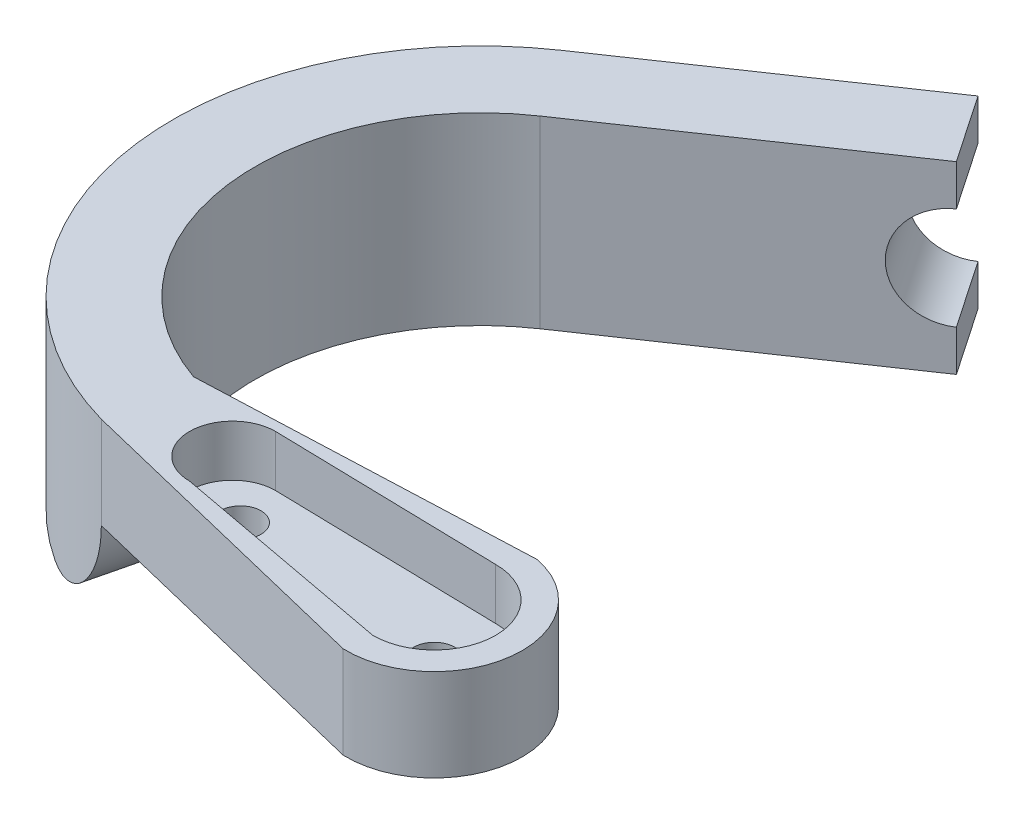
SolidWorks part; units mm, degrees
ref_plane "Front" through (0, 0, 0) normal (0, 0, 1) x (1, 0, 0)
ref_plane "Top" through (0, 0, 0) normal (0, 1, 0) x (1, 0, 0)
ref_plane "Right" through (0, 0, 0) normal (1, 0, 0) x (0, 0, -1)
sketch "草图1" plane through (0, 0, 0) normal (0, 1, 0) x (1, 0, 0)
  line L26 (-8.4405, 12.3999) -> (3.6631, 20.6388)
  line L27 (-6.1905, 9.0945) -> (5.9131, 17.3334)
  line L32 (11.5407, -18.2417) -> (-4.0757, -14.4357)
  line L33 (11.696, -13.9503) -> (1.196, -12.9105) construction
  line L34 (3.6631, 20.6388) -> (5.9131, 17.3334)
  line L35 (12.483, -9.7287) -> (-3.6175, -10.3897)
  arc A25 (-6.1905, 9.0945) -> (-3.6175, -10.3897) centre (0, 0) ccw
  arc A26 (-8.4405, 12.3999) -> (-3.0234, -14.6921) centre (0, 0) ccw
  arc A33 (11.5407, -18.2417) -> (12.483, -9.7287) centre (11.696, -13.9503) ccw
  circle A37 centre (11.696, -13.9503) radius 1
  circle A38 centre (1.196, -12.9105) radius 1
  point P0 (0, 0)
  point P13 (52.2746, -21.9905)
  dimension "D1" = 10.5
extrude "凸台-拉伸2" add sketch "草图1" along normal blind 9
sketch "草图4" plane through (0, 9, 0) normal (0, 1, 0) x (1, 0, 0)
  line L0 (11.696, -13.9503) -> (0.696, -12.8002) construction
  line L1 (11.696, -10.9503) -> (0.696, -10.6997)
  line L2 (11.696, -16.9503) -> (0.696, -14.9006)
  arc A0 (11.696, -16.9503) -> (11.696, -10.9503) centre (11.696, -13.9503) ccw
  arc A1 (0.7917, -10.7019) -> (0.696, -14.9006) centre (0.696, -12.8002) ccw
  dimension "D1" = 11
extrude "切除-拉伸3" cut sketch "草图4" against normal blind 2.5
sketch "草图5" plane through (-8.4405, 0, -12.3999) normal (-0.5627, 0, -0.8267) x (-0.8267, 0, 0.5627)
  line L0 (-14.6416, 9) -> (-14.6416, 0) construction
  circle A0 centre (-14.6416, 4.5) radius 2.5
extrude "切除-拉伸4" cut sketch "草图5" against normal blind 5
sketch "草图6" plane through (-3.5495, 0, 14.5639) normal (-0.2368, 0, 0.9716) x (0.9716, 0, 0.2368)
  line L0 (-0.5415, 9) -> (-0.5415, 0) construction
  line L1 (-0.5415, 4.5) -> (18.9609, 4.5)
  line L3 (-0.5415, 0) -> (18.9609, 0)
  line L4 (18.9609, 4.5) -> (18.9609, 0)
  line L5 (-15, 0) -> (-0.5415, 0) construction
  line L6 (-5.0415, 0) -> (-0.5415, 0)
  arc A0 (-0.5415, 4.5) -> (-5.0415, 0) centre (-5.0415, 4.5) cw
extrude "切除-拉伸5" cut sketch "草图6" against normal blind 10
